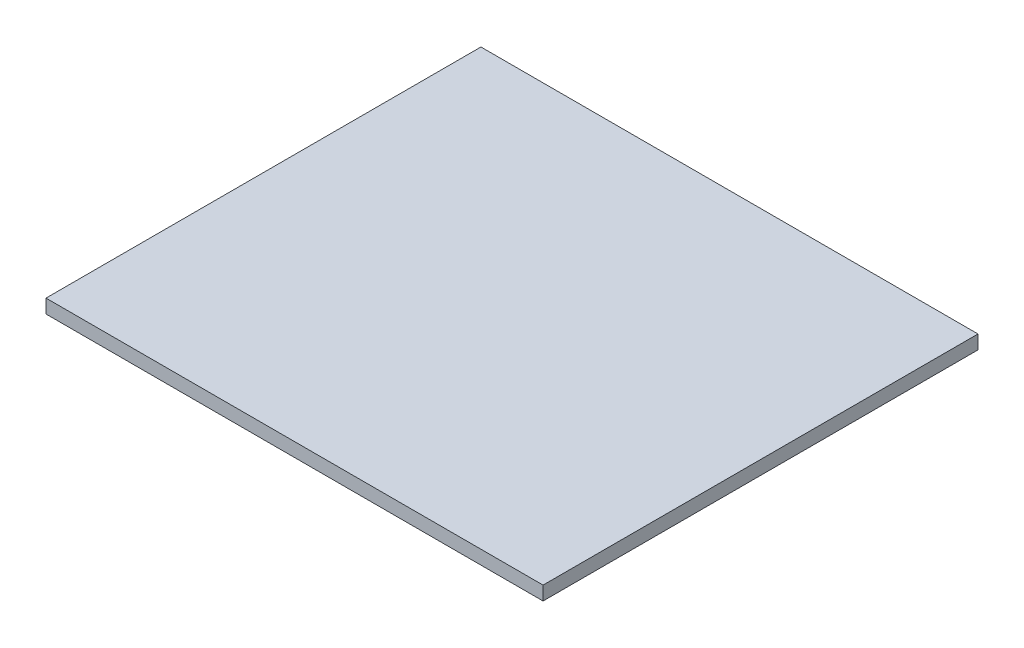
SolidWorks part; units mm, degrees
ref_plane "Front Plane" through (0, 0, 0) normal (0, 0, 1) x (1, 0, 0)
ref_plane "Top Plane" through (0, 0, 0) normal (0, 1, 0) x (1, 0, 0)
ref_plane "Right Plane" through (0, 0, 0) normal (1, 0, 0) x (0, 0, -1)
sketch "Sketch1" plane through (0, 0, 0) normal (0, 1, 0) x (1, 0, 0)
  line L1 (-360, -315) -> (360, -315)
  line L2 (-360, -315) -> (-360, 315)
  line L3 (-360, 315) -> (360, 315)
  line L4 (360, -315) -> (360, 315)
  line L5 (-360, -315) -> (360, 315) construction
  line L6 (-360, 315) -> (360, -315) construction
  point P0 (0, 0)
  dimension "D1" = 720
  dimension "D2" = 630
extrude "Boss-Extrude1" add sketch "Sketch1" along normal blind 20 contours L3 L4 L1 L2
